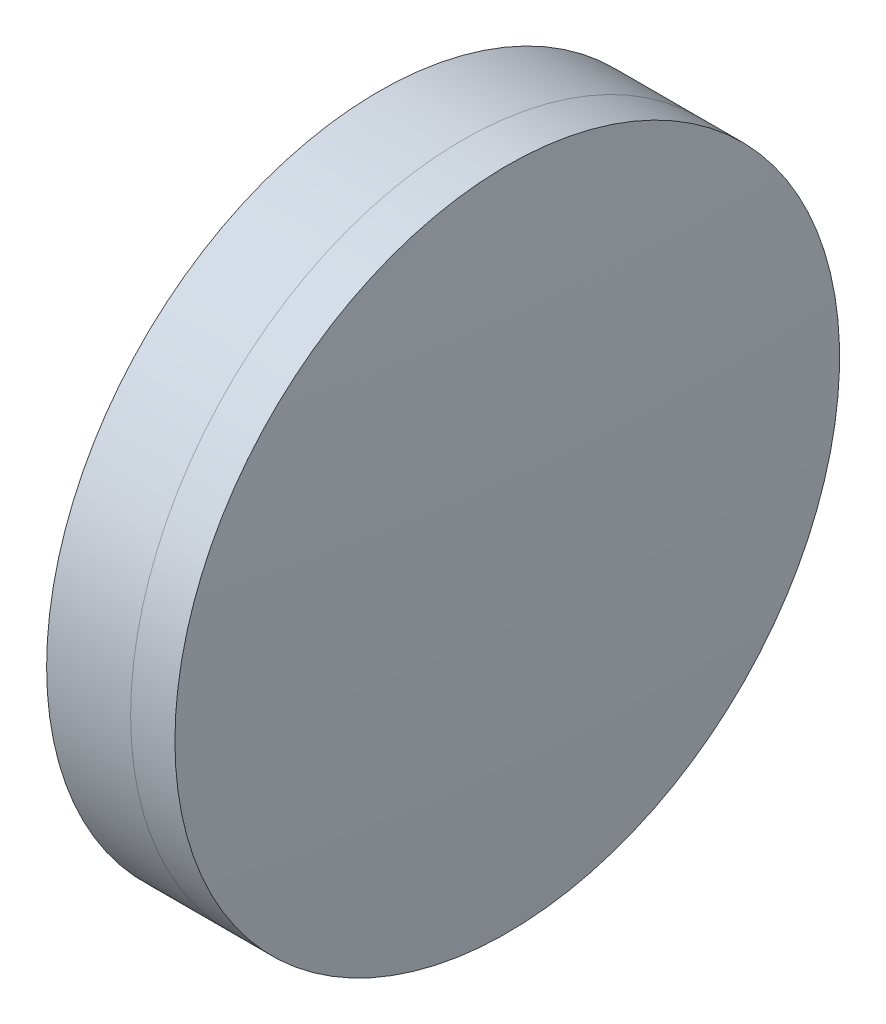
SolidWorks part; units mm, degrees
ref_plane "前视基准面" through (0, 0, 0) normal (0, 0, 1) x (1, 0, 0)
ref_plane "上视基准面" through (0, 0, 0) normal (0, 1, 0) x (1, 0, 0)
ref_plane "右视基准面" through (0, 0, 0) normal (1, 0, 0) x (0, 0, -1)
sketch "草图1" plane through (0, 0, 0) normal (0, 1, 0) x (1, 0, 0)
  line L0 (124.5233, 0) -> (646.9917, 0) construction
  line L1 (529.1954, -15) -> (532.9862, -15)
  line L2 (529.1954, 15) -> (532.9862, 15)
  arc A0 (532.9862, -15) -> (532.9862, 15) centre (317.207, 0) ccw
  arc A1 (529.1954, 15) -> (529.1954, -15) centre (579.507, 0) ccw
  point P10 (527.007, 0)
  point P11 (533.507, 0)
  dimension "D3" = 52.5
  dimension "D4" = 216.3
  dimension "D1" = 15
  dimension "D2" = 15
  dimension "D5" = 6.5
revolve "旋转1" add sketch "草图1" angle 360 about L0
sketch "草图2" plane through (0, 0, 0) normal (0, 1, 0) x (1, 0, 0)
  line L0 (-0.5519, 0) -> (622.6607, 0) construction
  line L2 (532.9862, 15) -> (534.9862, 15)
  line L3 (532.9862, -15) -> (534.9862, -15)
  arc A0 (534.9862, -15) -> (534.9862, 15) centre (319.207, 0) ccw
  arc A1 (532.9862, -15) -> (532.9862, 15) centre (317.207, 0) ccw construction
  arc A2 (532.9862, -15) -> (532.9862, 15) centre (317.207, 0) ccw
  point P4 (533.507, 0)
  point P8 (535.507, 0)
  dimension "D1" = 216.3
  dimension "D2" = 2
revolve "旋转3" add sketch "草图2" angle 360 about L0
